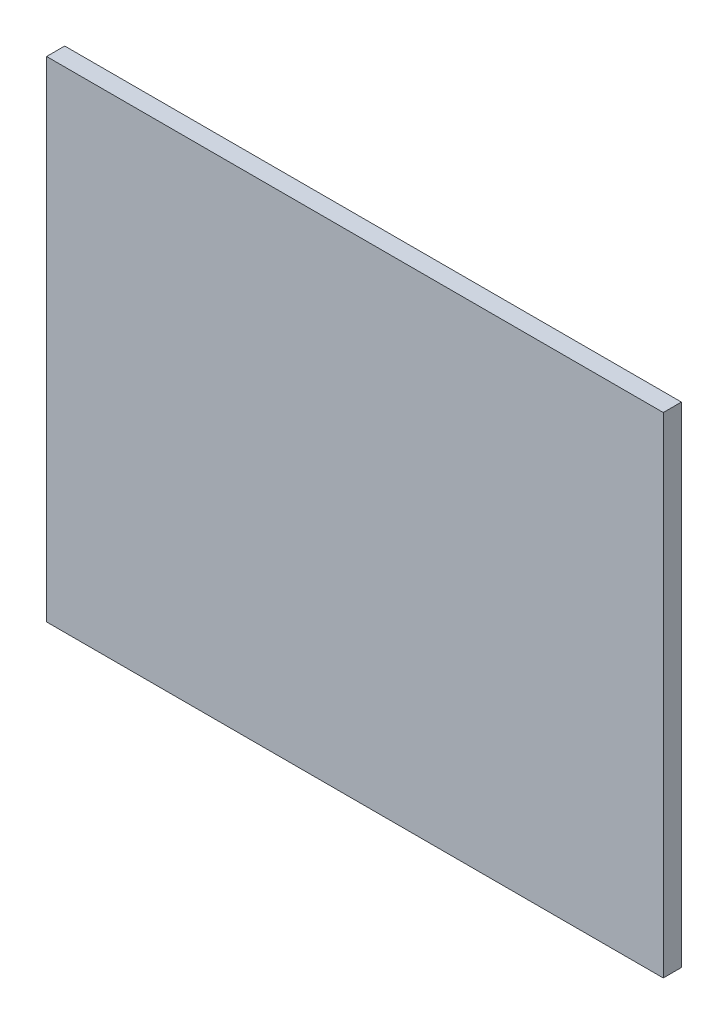
SolidWorks part; units mm, degrees
ref_plane "Front Plane" through (0, 0, 0) normal (0, 0, 1) x (1, 0, 0)
ref_plane "Top Plane" through (0, 0, 0) normal (0, 1, 0) x (1, 0, 0)
ref_plane "Right Plane" through (0, 0, 0) normal (1, 0, 0) x (0, 0, -1)
sketch "Sketch1" plane through (0, 0, 0) normal (0, 0, 1) x (1, 0, 0)
  line L1 (340, 270) -> (0, 270)
  line L2 (340, 270) -> (340, 0)
  line L3 (340, 0) -> (0, 0)
  line L4 (0, 270) -> (0, 0)
  dimension "D1" = 340
  dimension "D2" = 270
extrude "Boss-Extrude1" add sketch "Sketch1" along normal blind 10
